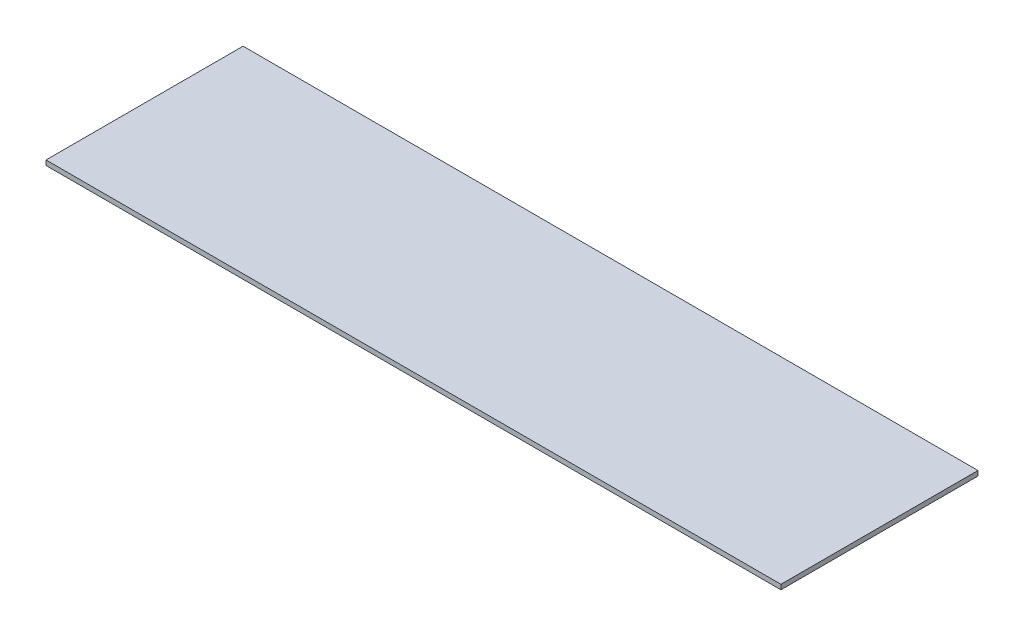
SolidWorks part; units mm, degrees
material "ABS"
ref_plane "Front" through (0, 0, 0) normal (0, 0, 1) x (1, 0, 0)
ref_plane "Top" through (0, 0, 0) normal (0, 1, 0) x (1, 0, 0)
ref_plane "Right" through (0, 0, 0) normal (1, 0, 0) x (0, 0, -1)
sketch "Sketch1" plane through (0, 0, 0) normal (0, 1, 0) x (1, 0, 0)
  line L1 (0, 0) -> (242.4, 0)
  line L2 (0, 0) -> (0, 65)
  line L3 (0, 65) -> (242.4, 65)
  line L4 (242.4, 0) -> (242.4, 65)
  dimension "D1" = 65
  dimension "D2" = 242.4
extrude "Boss-Extrude1" add sketch "Sketch1" along normal blind 1.5875
